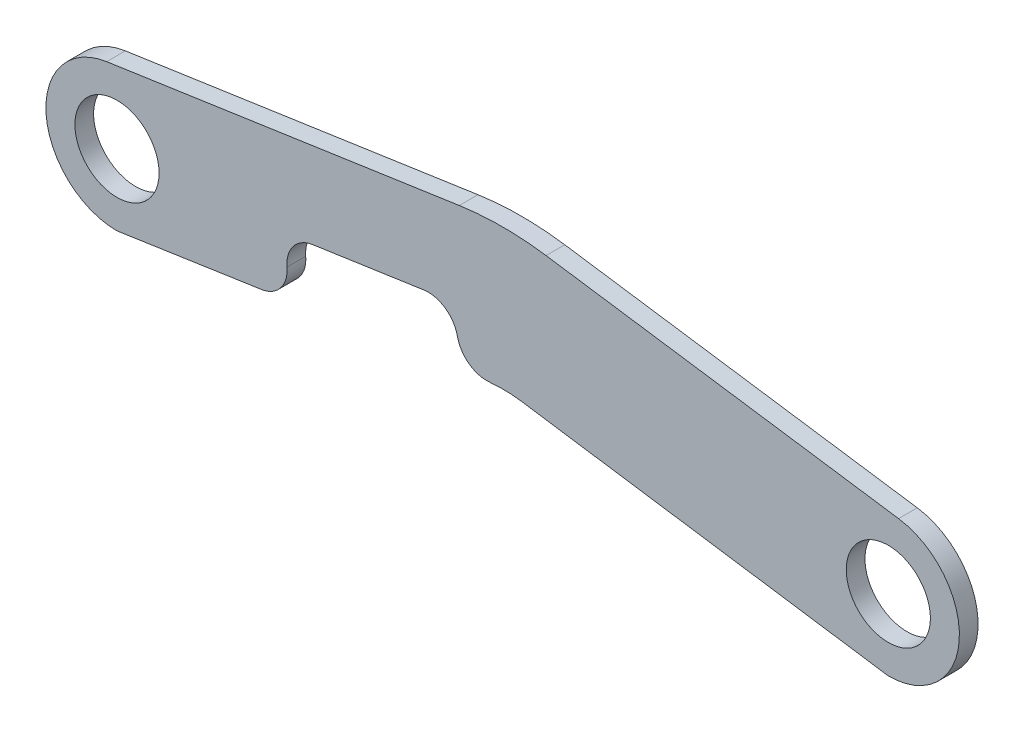
SolidWorks part; units mm, degrees
ref_plane "Front Plane" through (0, 0, 0) normal (0, 0, 1) x (1, 0, 0)
ref_plane "Top Plane" through (0, 0, 0) normal (0, 1, 0) x (1, 0, 0)
ref_plane "Right Plane" through (0, 0, 0) normal (1, 0, 0) x (0, 0, -1)
sketch "Sketch1" plane through (0, 0, 0) normal (0, 0, 1) x (1, 0, 0)
  line L7 (-265.3774, 23.8009) -> (-130.937, 43.5291)
  line L8 (-130.937, 43.5291) -> (3.4906, 23.8762)
  line L10 (-130.937, -4.7309) -> (0, -24.13)
  line L11 (-144.8835, -6.8049) -> (-147.6409, 11.9858)
  line L12 (-147.6409, 11.9858) -> (-205.5705, 3.485)
  line L13 (-205.5705, 3.485) -> (-202.7602, -15.4122)
  line L14 (-130.937, -4.7309) -> (-144.8835, -6.8049)
  line L15 (-202.7602, -15.4122) -> (-261.874, -24.2034)
  circle A2 centre (-261.874, -0.0734) radius 14.2875
  circle A3 centre (0, 0) radius 14.2875
  arc A6 (-265.3774, 23.8009) -> (-261.874, -24.2034) centre (-261.874, -0.0734) ccw
  arc A7 (3.4906, 23.8762) -> (0, -24.13) centre (0, 0) cw
  dimension "D1" = 48.26
  dimension "D2" = 28.575
extrude "Boss-Extrude1" add sketch "Sketch1" along normal blind 6.35
fillet "Fillet2" radius 101.6 1 edges at (-130.937, 43.5291, 3.175)
fillet "Fillet4" radius 10.16 1 edges at (-147.6409, 11.9858, 3.175)
fillet "Fillet5" radius 10.16 1 edges at (-205.5705, 3.485, 3.175)
fillet "Fillet6" radius 10.16 1 edges at (-202.7602, -15.4122, 3.175)
fillet "Fillet7" radius 43.18 1 edges at (-130.937, -4.7309, 3.175)
fillet "Fillet8" radius 10.16 1 edges at (-144.8835, -6.8049, 3.175)
